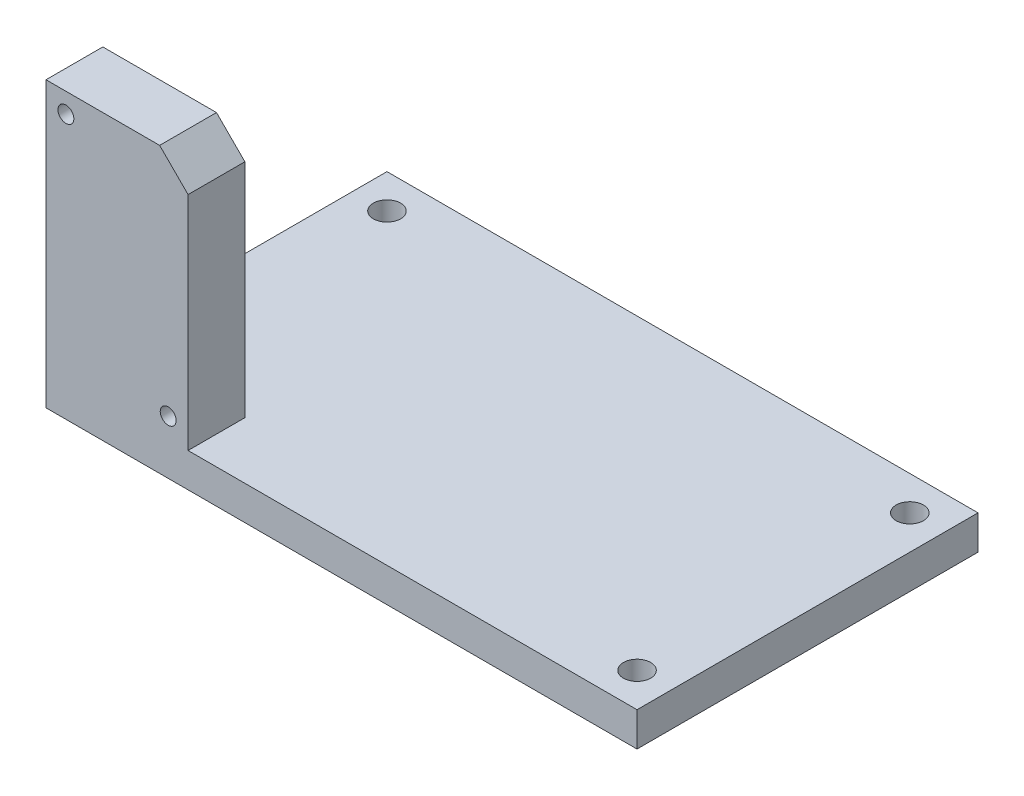
SolidWorks part; units mm, degrees
ref_plane "Front Plane" through (0, 0, 0) normal (0, 0, 1) x (1, 0, 0)
ref_plane "Top Plane" through (0, 0, 0) normal (0, 1, 0) x (1, 0, 0)
ref_plane "Right Plane" through (0, 0, 0) normal (1, 0, 0) x (0, 0, -1)
sketch "Sketch1" plane through (0, 0, 0) normal (0, 1, 0) x (1, 0, 0)
  line L0 (-6, -6) -> (98, -6)
  line L1 (0, 0) -> (92, 0) construction
  line L2 (0, 0) -> (0, 48) construction
  line L3 (0, 48) -> (92, 48) construction
  line L4 (92, 0) -> (92, 48) construction
  line L5 (98, -6) -> (98, 54)
  line L6 (-6, 54) -> (98, 54)
  line L7 (-6, -6) -> (-6, 54)
  circle A0 centre (0, 48) radius 2.4
  circle A1 centre (92, 48) radius 2.4
  circle A2 centre (92, 0) radius 2.4
  circle A3 centre (0, 0) radius 2.4
  dimension "D4" = 4.8
  dimension "D2" = 92
  dimension "D3" = 48
  dimension "D1" = 6
extrude "Boss-Extrude1" add sketch "Sketch1" along normal blind 6
sketch "Sketch2" plane through (0, 0, 6) normal (0, 0, 1) x (1, 0, 0)
  line L1 (-6, 6) -> (19, 6)
  line L2 (-6, 6) -> (-6, 50)
  line L3 (-6, 50) -> (19, 50)
  line L4 (19, 6) -> (19, 50)
  dimension "D1" = 44
  dimension "D2" = 25
extrude "Boss-Extrude2" add sketch "Sketch2" against normal blind 10
sketch "Sketch3" plane through (0, 0, -4) normal (0, 0, -1) x (-1, 0, 0)
  line L13 (2.5, 9.5) -> (2.5, 46.5)
  line L14 (2.5, 46.5) -> (-15.5, 46.5)
  line L15 (-15.5, 46.5) -> (-15.5, 9.5)
  line L16 (-15.5, 9.5) -> (2.5, 9.5)
  line L17 (2.5, 9.5) -> (2.5, 46.5) construction
  line L18 (2.5, 46.5) -> (-15.5, 46.5) construction
  line L19 (-15.5, 46.5) -> (-15.5, 9.5) construction
  line L20 (-15.5, 9.5) -> (2.5, 9.5) construction
  circle A0 centre (-15.5, 9.5) radius 1.4
  circle A1 centre (2.5, 46.5) radius 1.4
  dimension "D2" = 2.8
  dimension "D1" = 3.5
extrude "Cut-Extrude1" cut sketch "Sketch3" against normal through all
chamfer "Chamfer1" distance 5 angle 45 1 edges at (19, 50, 1)
